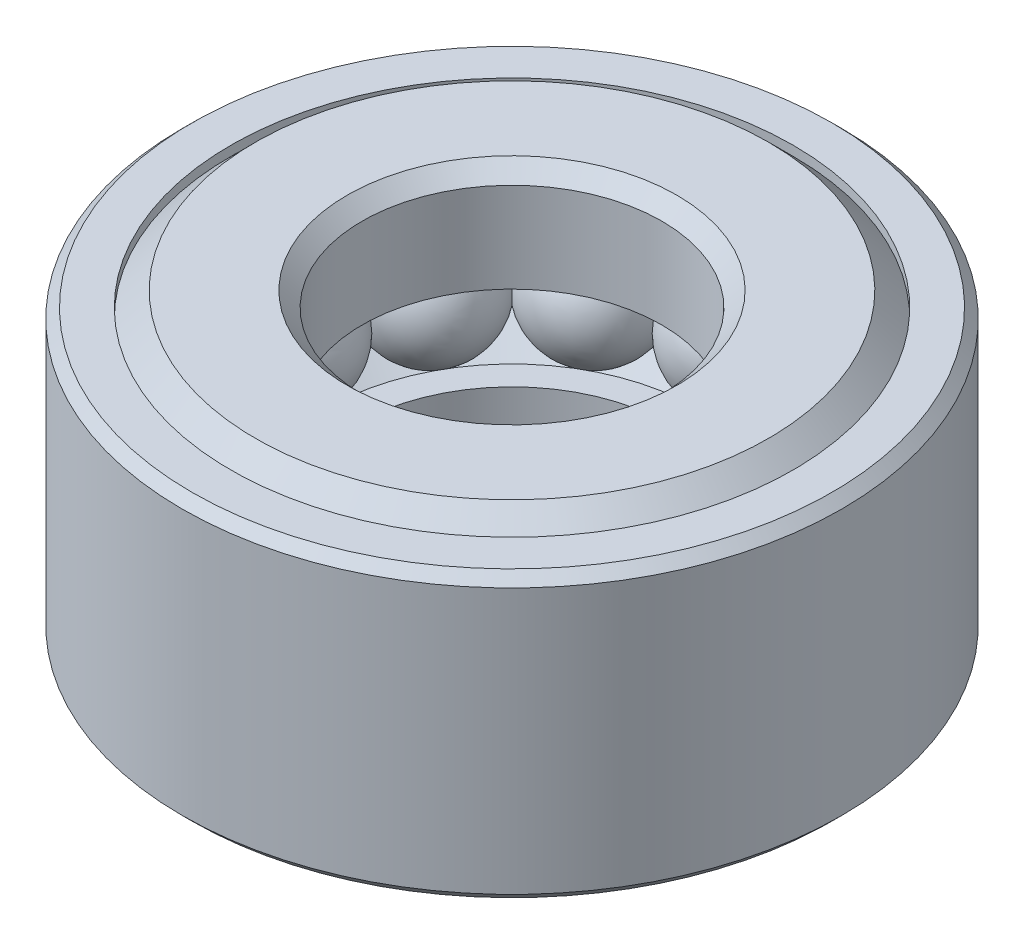
SolidWorks part; units mm, degrees
material "Plain Carbon Steel"
ref_plane "Front Plane" through (0, 0, 0) normal (0, 0, 1) x (1, 0, 0)
ref_plane "Top Plane" through (0, 0, 0) normal (0, 1, 0) x (1, 0, 0)
ref_plane "Right Plane" through (0, 0, 0) normal (1, 0, 0) x (0, 0, -1)
sketch "SketchA" plane through (0, 0, 0) normal (0, 1, 0) x (1, 0, 0)
  line L0 (-8.7312, 0) -> (8.7313, 0) construction
  line L1 (-3.9688, 0) -> (3.9688, 0) construction
  line L2 (-4.1656, 0) -> (4.1656, 0) construction
  circle A0 centre (0, 0) radius 8.7313 construction
  circle A1 centre (0, 0) radius 3.9688 construction
  circle A2 centre (0, 0) radius 4.1656 construction
  point P2 (0, 0)
  point P6 (0, 0)
  point P10 (0, 8.7313)
  point P11 (0, 3.9688)
  point P12 (0, -3.9688)
  point P13 (0, -8.7313)
  point P16 (0, 4.1656)
  point P17 (0, 0)
  point P19 (0, -4.1656)
  dimension "OD" = 17.4625
  dimension "ID" = 7.9375
  dimension "ID'" = 8.3312
sketch "Sketch1" plane through (0, 0, 0) normal (1, 0, 0) x (0, 0, -1)
  line L0 (-5.9571, 0) -> (5.9571, 0) construction
  line L1 (0, -3.9688) -> (0, 3.9687) construction
  line L2 (-6.7947, 3.9687) -> (-3.9688, 3.9687) construction
  line L3 (-7.0071, 1.1906) -> (-7.9454, 1.1906)
  line L4 (-7.9454, 1.1906) -> (-7.9454, 2.818)
  line L5 (-7.9454, 2.818) -> (-6.7947, 3.9687)
  line L6 (-3.9688, 3.9687) -> (-3.9688, 1.1906) construction
  line L7 (-3.9688, 1.1906) -> (-4.9071, 1.1906)
  line L8 (-5.9571, 0) -> (-5.9571, 0.3969) construction
  line L9 (-7.5446, 0) -> (-8.7312, 0) construction
  line L10 (-4.1656, -3.9687) -> (-4.1656, -1.1906) construction
  line L11 (-4.1656, -1.1906) -> (-4.9071, -1.1906)
  line L13 (-8.0328, -1.1906) -> (-8.0328, -3.7123)
  line L16 (-4.1656, -3.9687) -> (-7.7763, -3.9687) construction
  line L17 (-7.7763, -3.9687) -> (-8.0328, -3.7123)
  line L18 (-7.0071, 1.1906) -> (-5.9571, 2.1167)
  line L19 (-5.9571, 2.1167) -> (-4.9071, 1.1906)
  line L20 (-5.9571, 0.3969) -> (-5.9571, 0.7937) construction
  line L21 (-5.9571, 0.7937) -> (-5.9571, 1.1906) construction
  line L22 (-5.9571, 1.1906) -> (-5.9571, 1.5875) construction
  line L23 (-7.0071, -1.1906) -> (-5.9571, -2.1167)
  line L24 (-5.9571, -2.1167) -> (-4.9071, -1.1906)
  line L27 (-8.0328, -1.1906) -> (-7.7763, -1.1906) construction
  line L28 (-7.7763, -1.1906) -> (-7.5199, -1.1906) construction
  line L29 (-7.5199, -1.1906) -> (-7.2635, -1.1906) construction
  line L30 (-7.2635, -1.1906) -> (-7.0071, -1.1906) construction
  line L31 (-6.7947, 3.9687) -> (-4.3656, 3.9687)
  line L32 (-4.3656, 3.9687) -> (-3.9688, 3.5719)
  line L33 (-3.9688, 3.5719) -> (-3.9688, 1.1906)
  line L34 (-4.1656, -1.1906) -> (-4.1656, -3.5719)
  line L35 (-4.1656, -3.5719) -> (-4.5625, -3.9687)
  line L36 (-4.5625, -3.9687) -> (-7.7763, -3.9687)
  line L37 (-6.7947, 3.9687) -> (-6.7947, -3.9688) construction
  line L38 (6.7947, 3.9687) -> (6.7947, -3.9688) construction
  line L39 (8.7312, -3.9687) -> (8.7312, 3.9687) construction
  line L40 (8.7312, -3.9687) -> (-8.7312, -3.9687) construction
  line L41 (8.7312, 3.9687) -> (6.7947, 3.9687) construction
  line L43 (4.1656, -3.9687) -> (4.1656, -1.1906) construction
  line L44 (3.9688, 3.9687) -> (3.9688, 1.1906) construction
  circle A0 centre (-5.9571, 0) radius 1.5875 construction
  arc A1 (-4.9071, 1.1906) -> (-7.0071, 1.1906) centre (-5.9571, 0) ccw construction
  arc A2 (-4.9071, -1.1906) -> (-7.0071, -1.1906) centre (-5.9571, 0) cw construction
  point P15 (-5.9571, 1.1906)
  point P17 (0, 3.5719)
  point P46 (0, -3.9687)
  dimension "Ball Dia" = 3.175
  dimension "D1" = 45
  dimension "D3" = 16.0655
  dimension "D4" = 7.5406
  dimension "D5" = 45
  dimension "D2" = 15.8909
  dimension "D6" = 45
  dimension "D7" = 45
  dimension "D8" = 0.3969
  dimension "ID" = 8.3312
  dimension "D9" = 17.4625
  dimension "Thickness" = 7.9375
  dimension "D10" = 7.9375
sketch "Sketch7" plane through (0, 0, 0) normal (1, 0, 0) x (0, 0, -1)
  line L0 (-4.1656, -1.1906) -> (-4.9071, -1.1906) construction
  line L3 (-7.7763, -3.9687) -> (-8.0328, -3.7123) construction
  line L4 (-8.0328, -1.1906) -> (-8.0328, -3.7123) construction
  line L5 (-6.7947, 3.9687) -> (-4.3656, 3.9687)
  line L6 (-3.9688, 1.1906) -> (-4.9071, 1.1906) construction
  line L9 (-7.9454, 2.818) -> (-6.7947, 3.9687) construction
  line L10 (-7.9454, 1.1906) -> (-7.9454, 2.818) construction
  line L11 (-7.0071, 1.1906) -> (-7.9454, 1.1906) construction
  line L12 (-4.1656, -1.1906) -> (-4.9071, -1.1906)
  line L15 (-7.7763, -3.9687) -> (-8.0328, -3.7123)
  line L16 (-8.0328, -1.1906) -> (-8.0328, -3.7123)
  line L18 (-3.9688, 1.1906) -> (-4.9071, 1.1906)
  line L21 (-7.9454, 2.818) -> (-6.7947, 3.9687)
  line L22 (-7.9454, 1.1906) -> (-7.9454, 2.818)
  line L23 (-7.0071, 1.1906) -> (-7.9454, 1.1906)
  line L24 (-7.0071, -1.1906) -> (-5.9571, -2.1167) construction
  line L25 (-5.9571, -2.1167) -> (-4.9071, -1.1906) construction
  line L26 (-5.9571, 2.1167) -> (-4.9071, 1.1906) construction
  line L27 (-7.0071, 1.1906) -> (-5.9571, 2.1167) construction
  line L28 (-7.0071, -1.1906) -> (-5.9571, -2.1167)
  line L29 (-5.9571, -2.1167) -> (-4.9071, -1.1906)
  line L30 (-5.9571, 2.1167) -> (-4.9071, 1.1906)
  line L31 (-7.0071, 1.1906) -> (-5.9571, 2.1167)
  line L32 (-8.0328, -1.1906) -> (-7.0071, -1.1906)
  line L33 (-4.3656, 3.9687) -> (-3.9687, 3.5719)
  line L34 (-3.9687, 3.5719) -> (-3.9688, 1.1906)
  line L35 (-4.1656, -1.1906) -> (-4.1656, -3.5719)
  line L36 (-4.1656, -3.5719) -> (-4.5625, -3.9687)
  line L37 (-4.5625, -3.9687) -> (-7.7763, -3.9687)
  arc A0 (-7.0071, -1.1906) -> (-4.9071, -1.1906) centre (-5.9571, 0) ccw construction
  arc A1 (-4.9071, 1.1906) -> (-7.0071, 1.1906) centre (-5.9571, 0) ccw construction
  arc A2 (-7.0071, -1.1906) -> (-4.9071, -1.1906) centre (-5.9571, 0) ccw construction
  arc A3 (-4.9071, 1.1906) -> (-7.0071, 1.1906) centre (-5.9571, 0) ccw construction
revolve "Revolve4" add sketch "Sketch7" angle 360 about L1
sketch "Sketch3" plane through (0, 0, 0) normal (1, 0, 0) x (0, 0, -1)
  line L0 (-5.9571, 1.5875) -> (-5.9571, -1.5875)
  arc A0 (-7.0071, -1.1906) -> (-4.9071, -1.1906) centre (-5.9571, 0) ccw construction
  arc A1 (-5.9571, 1.5875) -> (-5.9571, -1.5875) centre (-5.9571, 0) ccw
revolve "Revolve2" add sketch "Sketch3" angle 360 about L0
pattern_circular "CirPattern1" count 12 over 360 about axis through (0, 0, 0) along (0, 1, 0) of bodies 171
sketch "Sketch4" plane through (0, 0, 0) normal (1, 0, 0) x (0, 0, -1)
  line L0 (-8.7312, 3.5719) -> (-8.7312, -3.9688) construction
  line L1 (-8.7312, 3.5719) -> (-7.1916, 3.5719) construction
  line L2 (-7.9454, 2.818) -> (-6.7947, 3.9687) construction
  line L3 (-8.7312, 3.3155) -> (-8.7312, -3.7123) construction
  line L4 (-8.7312, 3.3155) -> (-7.448, 3.3155) construction
  line L5 (-8.0328, -3.9688) -> (-8.0328, 2.818) construction
  line L6 (-8.7312, -3.7123) -> (-8.4748, -3.9688) construction
  line L7 (-8.4748, -3.9688) -> (-8.0328, -3.9688) construction
  line L8 (-7.1916, 3.5719) -> (-8.4748, 3.5719) construction
  line L9 (-8.4748, 3.5719) -> (-8.7312, 3.3155) construction
  line L10 (-7.448, 3.5719) -> (-7.448, 3.3155) construction
  line L11 (-8.4748, 3.5719) -> (-7.448, 3.5719) construction
  line L12 (-7.448, 3.3155) -> (-7.9454, 2.818) construction
  line L13 (-8.0328, 2.818) -> (-7.9454, 2.818) construction
  line L14 (-8.7312, 3.3155) -> (-8.7312, -3.7123) construction
  line L15 (-7.448, 3.3155) -> (-8.0328, 3.3155)
  line L16 (-8.0328, 3.3155) -> (-8.0328, -3.9688)
  line L17 (-7.448, 3.3155) -> (-7.448, 3.5719)
  line L18 (-7.448, 3.5719) -> (-8.4748, 3.5719)
  line L19 (-8.4748, 3.5719) -> (-8.7312, 3.3155)
  line L20 (-8.7312, 3.3155) -> (-8.7312, -3.7123)
  line L21 (-8.7312, -3.7123) -> (-8.4748, -3.9688)
  line L22 (-8.4748, -3.9688) -> (-8.0328, -3.9688)
  dimension "D1" = 45
revolve "Revolve3" add sketch "Sketch4" angle 360 about L1
sketch "Sketch8" plane through (0, 0, 0) normal (1, 0, 0) x (0, 0, -1)
  line L0 (-4.3656, 3.9687) -> (-3.9688, 3.5719) construction
  line L1 (-3.9688, 1.1906) -> (-4.9071, 1.1906) construction
  line L2 (-4.9071, 1.1906) -> (-5.9571, 2.1167) construction
  line L3 (-5.9571, 2.1167) -> (-7.0071, 1.1906) construction
  line L4 (-7.0071, 1.1906) -> (-7.9454, 1.1906) construction
  line L5 (-7.9454, 1.1906) -> (-7.9454, 2.818) construction
  line L6 (-7.9454, 2.818) -> (-7.1916, 3.5719) construction
  line L7 (-7.9454, 2.818) -> (-6.7947, 3.9687) construction
  line L8 (-3.9688, 3.5719) -> (-3.9688, 1.1906) construction
  line L11 (-4.1656, -1.1906) -> (-4.9071, -1.1906) construction
  line L12 (-4.9071, -1.1906) -> (-5.9571, -2.1167) construction
  line L13 (-5.9571, -2.1167) -> (-7.0071, -1.1906) construction
  line L14 (-7.0071, -1.1906) -> (-8.0328, -1.1906) construction
  line L15 (-8.0328, -1.1906) -> (-8.0328, -3.7123) construction
  line L16 (-8.0328, -3.7123) -> (-7.7763, -3.9687) construction
  line L17 (0, 3.9687) -> (0, -3.9688) construction
  line L18 (8.0328, -3.7123) -> (7.7763, -3.9687) construction
  line L19 (8.0328, -1.1906) -> (8.0328, -3.7123) construction
  line L20 (7.0071, -1.1906) -> (8.0328, -1.1906) construction
  line L21 (5.9571, -2.1167) -> (7.0071, -1.1906) construction
  line L22 (4.9071, -1.1906) -> (5.9571, -2.1167) construction
  line L23 (4.1656, -1.1906) -> (4.9071, -1.1906) construction
  line L26 (3.9688, 3.5719) -> (3.9688, 1.1906) construction
  line L27 (7.9454, 2.818) -> (7.1916, 3.5719) construction
  line L28 (7.9454, 1.1906) -> (7.9454, 2.818) construction
  line L29 (7.0071, 1.1906) -> (7.9454, 1.1906) construction
  line L30 (5.9571, 2.1167) -> (7.0071, 1.1906) construction
  line L31 (4.9071, 1.1906) -> (5.9571, 2.1167) construction
  line L32 (3.9688, 1.1906) -> (4.9071, 1.1906) construction
  line L33 (4.3656, 3.9687) -> (3.9688, 3.5719) construction
  line L34 (-4.1656, -1.1906) -> (-4.1656, -3.5719) construction
  line L35 (-4.1656, -3.5719) -> (-4.5625, -3.9687) construction
  line L36 (4.1656, -3.5719) -> (4.5625, -3.9687) construction
  line L37 (4.1656, -1.1906) -> (4.1656, -3.5719) construction
  circle A0 centre (-5.9571, 0) radius 1.5875 construction
  circle A2 centre (-5.9571, 0) radius 1.5875 construction
  circle A3 centre (5.9571, 0) radius 1.5875 construction
equation "\"D3@Sketch1\"=\"OD@SketchA\"*.92"
equation "\"D4@Sketch1\"=.95*\"Thickness@Sketch1\""
equation "\"D2@Sketch1\"=\"OD@SketchA\"*.91"
equation "\"D8@Sketch1\"=\"Ball Dia@Sketch1\"*.125"
equation "\"ID@Sketch1\"=\"ID'@SketchA\""
equation "\"D9@Sketch1\"=\"OD@SketchA\""
equation "\"D10@Sketch1\"=\"ID@SketchA\""
